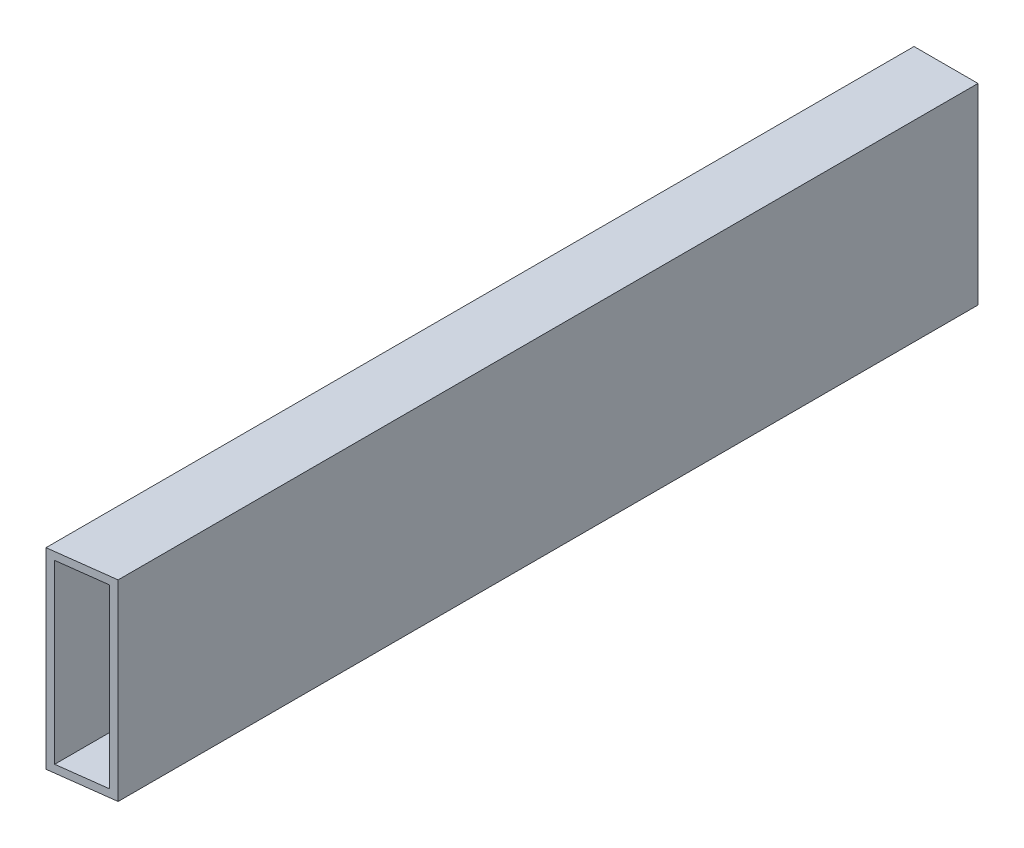
SolidWorks part; units mm, degrees
material "A500"
ref_plane "Front Plane" through (0, 0, 0) normal (0, 0, 1) x (1, 0, 0)
ref_plane "Top Plane" through (0, 0, 0) normal (0, 1, 0) x (1, 0, 0)
ref_plane "Right Plane" through (0, 0, 0) normal (1, 0, 0) x (0, 0, -1)
sketch "Sketch2" plane through (0, 0, 0) normal (0, 0, 1) x (1, 0, 0)
  line L0 (0, 0) -> (0, 38.1)
  line L1 (0, 38.1) -> (12.7, 38.1)
  line L2 (12.7, 38.1) -> (12.7, 0)
  line L3 (12.7, 0) -> (0, 0)
  line L4 (12.7, -38.1) -> (12.7, -35.052)
  line L5 (0, 0) -> (-12.7, 0)
  line L6 (0, 0) -> (0, -38.1)
  line L7 (0, -38.1) -> (-12.7, -38.1)
  line L8 (-12.7, 0) -> (-12.7, -38.1)
  line L9 (-12.7, -38.1) -> (12.7, -38.1)
  line L10 (-12.7, -38.1) -> (-12.7, 38.1)
  line L11 (-12.7, 38.1) -> (12.7, 38.1)
  line L12 (12.7, -38.1) -> (12.7, 38.1)
  line L13 (12.7, -35.052) -> (9.652, -35.052)
  line L14 (-12.7, 38.1) -> (-9.652, 38.1)
  line L15 (-9.652, 38.1) -> (-9.652, 35.052)
  line L17 (-9.652, 35.052) -> (9.652, 35.052)
  line L18 (-9.652, 35.052) -> (-9.652, -35.052)
  line L19 (-9.652, -35.052) -> (9.652, -35.052)
  line L20 (9.652, 35.052) -> (9.652, -35.052)
  dimension "D1" = 38.1
  dimension "D2" = 12.7
  dimension "D3" = 38.1
  dimension "D4" = 12.7
  dimension "D5" = 3.048
  dimension "D6" = 3.048
  dimension "D7" = 3.048
  dimension "D8" = 3.048
extrude "Boss-Extrude1" add sketch "Sketch2" along normal up to vertex (322.3727 mm away) contours L18 L15 L11 L10 L5 | L15 L17 L0 L11 | L17 L20 L3 L2 L1 L0 | L3 L20 L13 L12 | L19 L18 L5 L8 L7 L6 | L19 L6 L9 L4 L13
sketch "Sketch3" plane through (0, 0, 343) normal (0, 0, 1) x (1, 0, 0)
  line L1 (12.7, -38.1) -> (-12.7, -38.1)
  line L2 (12.7, -38.1) -> (12.7, 38.1)
  line L3 (12.7, 38.1) -> (-12.7, 38.1)
  line L4 (-12.7, -38.1) -> (-12.7, 38.1)
  line L5 (9.652, -35.052) -> (-9.652, -35.052)
  line L6 (9.652, -35.052) -> (9.652, 35.052)
  line L7 (9.652, 35.052) -> (-9.652, 35.052)
  line L8 (-9.652, -35.052) -> (-9.652, 35.052)
extrude "Boss-Extrude2" add sketch "Sketch3" along normal blind 50
sketch "Sketch5" plane through (0, 38.1, 0) normal (0, 1, 0) x (1, 0, 0)
  line L1 (12.534, -391.4035) -> (0, -343)
  line L8 (0, -343) -> (19.8, -419.4631) construction
  line L9 (0, -293) -> (0, -343)
  line L10 (0, 0) -> (0, -343) construction
  line L11 (12.534, -391.4035) -> (75.5598, -333.3757)
  line L12 (75.5598, -333.3757) -> (0, -293)
  line L15 (75.5598, -333.3757) -> (-33.0773, -347.2132)
  line L16 (75.5598, -333.3757) -> (83.797, -398.0452)
  line L17 (-33.0773, -347.2132) -> (-24.8401, -411.8827)
  line L18 (83.797, -398.0452) -> (-24.8401, -411.8827)
  dimension "D1" = 50
  dimension "D2" = 50
extrude "Cut-Extrude2" cut sketch "Sketch5" against normal through all both and the other way through all
equation "\"D3@Sketch2\"=\"D1@Sketch2\""
equation "\"D4@Sketch2\"=\"D2@Sketch2\""
